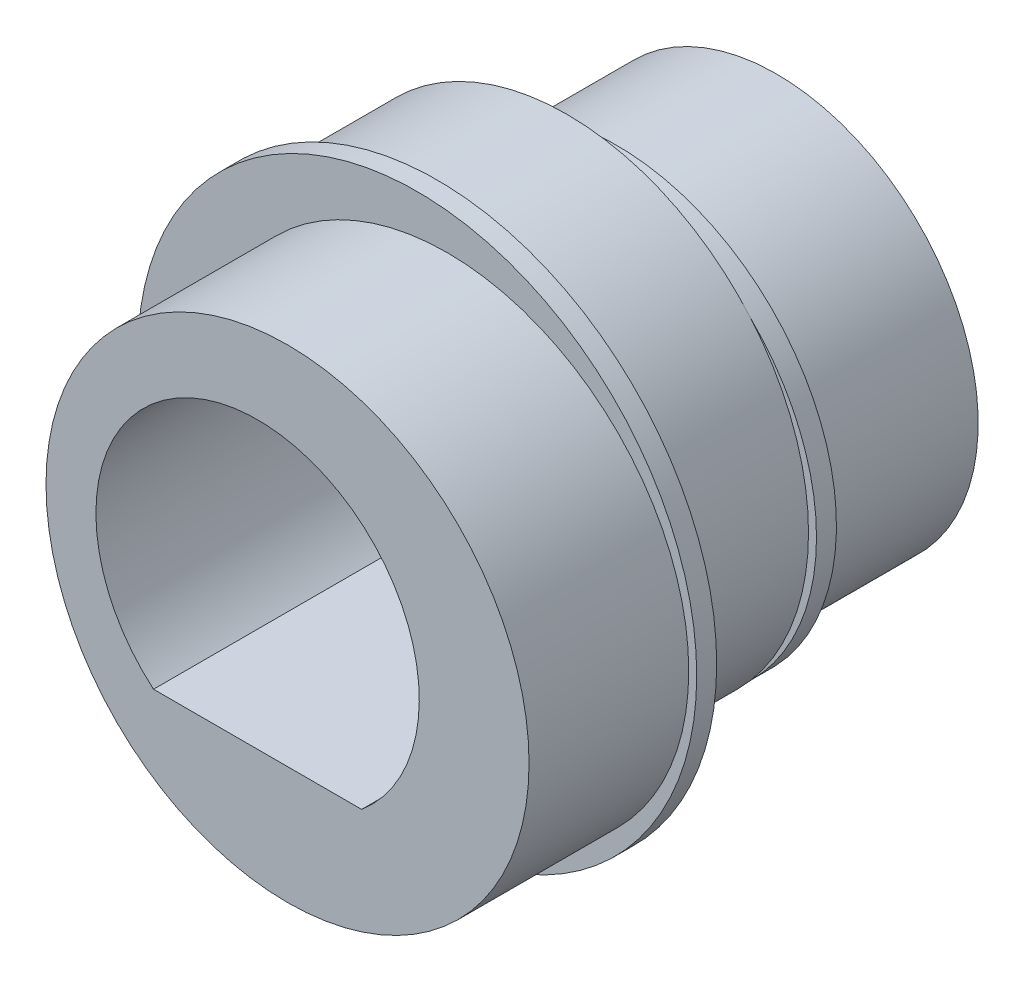
SolidWorks part; units mm, degrees
ref_plane "前视基准面" through (0, 0, 0) normal (0, 0, 1) x (1, 0, 0)
ref_plane "上视基准面" through (0, 0, 0) normal (0, 1, 0) x (1, 0, 0)
ref_plane "右视基准面" through (0, 0, 0) normal (1, 0, 0) x (0, 0, -1)
sketch "草图1" plane through (0, 0, 0) normal (0, 0, 1) x (1, 0, 0)
  circle A0 centre (0, 0) radius 6.05 construction
  circle A1 centre (-0.75, 0) radius 6.05
  dimension "D1" = 12.1
  dimension "D2" = 0.75
extrude "凸台-拉伸1" add sketch "草图1" along normal blind 4
sketch "草图2" plane through (0, 0, 4) normal (0, 0, 1) x (1, 0, 0)
  circle A1 centre (0, 0) radius 7
  dimension "D1" = 14
extrude "凸台-拉伸2" add sketch "草图2" along normal blind 0.5
sketch "草图3" plane through (0, 0, 4.5) normal (0, 0, 1) x (1, 0, 0)
  circle A0 centre (0.75, 0) radius 6.05
  circle A1 centre (0, 0) radius 6.05 construction
  dimension "D1" = 0.75
extrude "凸台-拉伸3" add sketch "草图3" along normal blind 4
sketch "草图5" plane through (0, 0, 0) normal (0, 0, -1) x (-1, 0, 0)
  circle A0 centre (0, 0) radius 5.5
  dimension "D1" = 11
extrude "凸台-拉伸4" add sketch "草图5" along normal blind 0.5
sketch "草图6" plane through (0, 0, -0.5) normal (0, 0, -1) x (-1, 0, 0)
  circle A0 centre (0, 0) radius 5.05
  dimension "D1" = 10.1
extrude "凸台-拉伸5" add sketch "草图6" along normal blind 4
sketch "草图4" plane through (0, 0, 8.5) normal (0, 0, 1) x (1, 0, 0)
  line L0 (-2.6062, -3.1) -> (2.6062, -3.1)
  circle A0 centre (0, 0) radius 4.05
  point P5 (0, 0)
  point P7 (0, 0)
  dimension "D1" = 8.1
  dimension "D2" = 3.1
extrude "切除-拉伸1" cut sketch "草图4" against normal through all contours L0 A0
